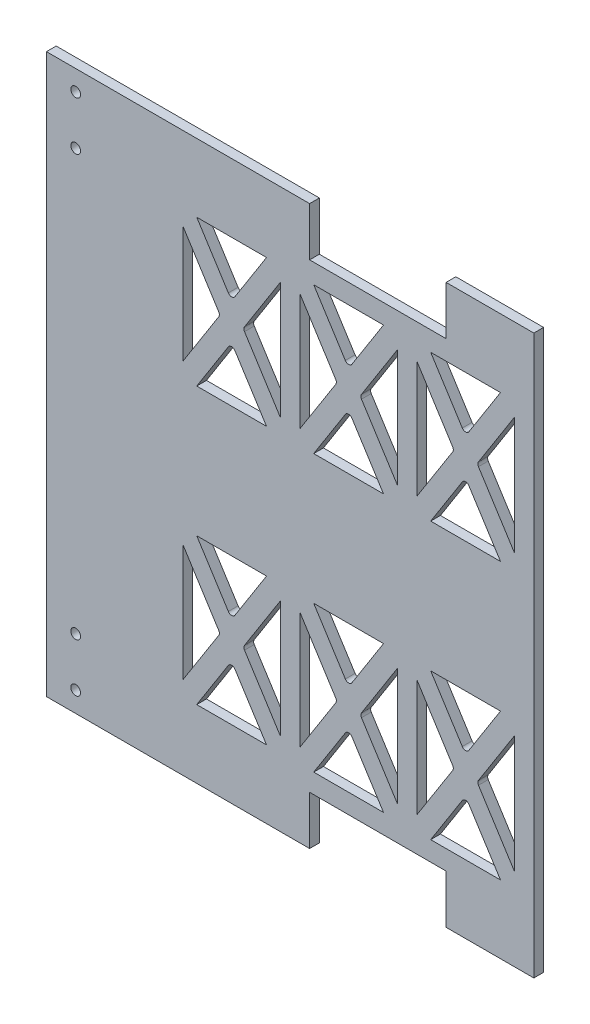
SolidWorks part; units mm, degrees
material "Acrylic (Medium-high impact)"
ref_plane "Front Plane" through (0, 0, 0) normal (0, 0, 1) x (1, 0, 0)
ref_plane "Top Plane" through (0, 0, 0) normal (0, 1, 0) x (1, 0, 0)
ref_plane "Right Plane" through (0, 0, 0) normal (1, 0, 0) x (0, 0, -1)
sketch "Sketch2" plane through (0, 0, 0) normal (0, 0, 1) x (1, 0, 0)
  line L1 (-125, 143.25) -> (125, 143.25)
  line L2 (-125, 143.25) -> (-125, -143.25)
  line L3 (-125, -143.25) -> (125, -143.25)
  line L4 (125, 143.25) -> (125, -143.25)
  line L5 (-125, 143.25) -> (125, -143.25) construction
  line L6 (-125, -143.25) -> (125, 143.25) construction
  point P0 (0, 0)
  dimension "D1" = 250
  dimension "D2" = 286.5
extrude "Boss-Extrude1" add sketch "Sketch2" along normal blind 5
sketch "Sketch3" plane through (0, 0, 5) normal (0, 0, 1) x (1, 0, 0)
  line L0 (-125, 143.25) -> (-125, -143.25) construction
  line L1 (125, 143.25) -> (-125, 143.25) construction
  line L2 (-125, -143.25) -> (125, -143.25) construction
  line L3 (-125, 0) -> (125, 0) construction
  line L4 (125, -143.25) -> (125, 143.25) construction
  line L5 (10, 143.25) -> (80, 143.25)
  line L6 (10, 143.25) -> (10, 118.25)
  line L7 (10, 118.25) -> (80, 118.25)
  line L8 (80, 143.25) -> (80, 118.25)
  line L9 (10, -118.25) -> (80, -118.25)
  line L10 (80, -143.25) -> (80, -118.25)
  line L11 (10, -143.25) -> (80, -143.25)
  line L12 (10, -143.25) -> (10, -118.25)
  line L13 (107.9031, 108.25) -> (91.6881, 82.7301)
  line L14 (65, 108.25) -> (115, 108.25)
  line L15 (65, 108.25) -> (65, 33.25)
  line L16 (65, 33.25) -> (115, 33.25)
  line L17 (115, 108.25) -> (115, 33.25)
  line L18 (72.0969, 33.25) -> (88.3119, 58.7699)
  line L19 (65, 70.75) -> (115, 70.75) construction
  line L20 (72.0969, 108.25) -> (88.3119, 82.7301)
  line L21 (107.9031, 33.25) -> (91.6881, 58.7699)
  line L22 (96.6054, 69.6774) -> (115, 40.7272)
  line L23 (83.3946, 71.8226) -> (65, 100.7728)
  line L24 (83.3946, 69.6774) -> (65, 40.7272)
  line L25 (96.6054, 71.8226) -> (115, 100.7728)
  line L26 (5, 108.25) -> (5, 33.25)
  line L27 (5, 108.25) -> (55, 108.25)
  line L28 (55, 108.25) -> (55, 33.25)
  line L29 (5, 33.25) -> (55, 33.25)
  line L30 (12.0969, 33.25) -> (28.3119, 58.7699)
  line L31 (23.3946, 69.6774) -> (5, 40.7272)
  line L32 (47.9031, 33.25) -> (31.6881, 58.7699)
  line L33 (36.6054, 69.6774) -> (55, 40.7272)
  line L34 (36.6054, 71.8226) -> (55, 100.7728)
  line L35 (47.9031, 108.25) -> (31.6881, 82.7301)
  line L36 (12.0969, 108.25) -> (28.3119, 82.7301)
  line L37 (23.3946, 71.8226) -> (5, 100.7728)
  line L38 (-55, 108.25) -> (-55, 33.25)
  line L39 (-55, 108.25) -> (-5, 108.25)
  line L40 (-5, 108.25) -> (-5, 33.25)
  line L41 (-55, 33.25) -> (-5, 33.25)
  line L42 (-47.9031, 33.25) -> (-31.6881, 58.7699)
  line L43 (-36.6054, 69.6774) -> (-55, 40.7272)
  line L44 (-12.0969, 33.25) -> (-28.3119, 58.7699)
  line L45 (-23.3946, 69.6774) -> (-5, 40.7272)
  line L46 (-23.3946, 71.8226) -> (-5, 100.7728)
  line L47 (-12.0969, 108.25) -> (-28.3119, 82.7301)
  line L48 (-47.9031, 108.25) -> (-31.6881, 82.7301)
  line L49 (-36.6054, 71.8226) -> (-55, 100.7728)
  line L62 (5, -33.25) -> (5, -108.25)
  line L63 (5, -33.25) -> (55, -33.25)
  line L64 (55, -33.25) -> (55, -108.25)
  line L65 (5, -108.25) -> (55, -108.25)
  line L66 (12.0969, -108.25) -> (28.3119, -82.7301)
  line L67 (23.3946, -71.8226) -> (5, -100.7728)
  line L68 (47.9031, -108.25) -> (31.6881, -82.7301)
  line L69 (36.6054, -71.8226) -> (55, -100.7728)
  line L70 (36.6054, -69.6774) -> (55, -40.7272)
  line L71 (47.9031, -33.25) -> (31.6881, -58.7699)
  line L72 (12.0969, -33.25) -> (28.3119, -58.7699)
  line L73 (23.3946, -69.6774) -> (5, -40.7272)
  line L74 (-55, -33.25) -> (-55, -108.25)
  line L75 (-55, -33.25) -> (-5, -33.25)
  line L76 (-5, -33.25) -> (-5, -108.25)
  line L77 (-55, -108.25) -> (-5, -108.25)
  line L78 (-47.9031, -108.25) -> (-31.6881, -82.7301)
  line L79 (-36.6054, -71.8226) -> (-55, -100.7728)
  line L80 (-12.0969, -108.25) -> (-28.3119, -82.7301)
  line L81 (-23.3946, -71.8226) -> (-5, -100.7728)
  line L82 (-23.3946, -69.6774) -> (-5, -40.7272)
  line L83 (-12.0969, -33.25) -> (-28.3119, -58.7699)
  line L84 (-47.9031, -33.25) -> (-31.6881, -58.7699)
  line L85 (-36.6054, -69.6774) -> (-55, -40.7272)
  line L98 (65, -33.25) -> (65, -108.25)
  line L99 (65, -33.25) -> (115, -33.25)
  line L100 (115, -33.25) -> (115, -108.25)
  line L101 (65, -108.25) -> (115, -108.25)
  line L102 (72.0969, -108.25) -> (88.3119, -82.7301)
  line L103 (83.3946, -71.8226) -> (65, -100.7728)
  line L104 (107.9031, -108.25) -> (91.6881, -82.7301)
  line L105 (96.6054, -71.8226) -> (115, -100.7728)
  line L106 (96.6054, -69.6774) -> (115, -40.7272)
  line L107 (107.9031, -33.25) -> (91.6881, -58.7699)
  line L108 (72.0969, -33.25) -> (88.3119, -58.7699)
  line L109 (83.3946, -69.6774) -> (65, -40.7272)
  line L110 (-115, -33.25) -> (-65, -33.25) [skipped]
  line L111 (-96.6054, -71.8226) -> (-115, -100.7728) [skipped]
  line L112 (-83.3946, -71.8226) -> (-65, -100.7728) [skipped]
  line L113 (-83.3946, -69.6774) -> (-65, -40.7272) [skipped]
  line L114 (-72.0969, -33.25) -> (-88.3119, -58.7699) [skipped]
  line L115 (-107.9031, -33.25) -> (-91.6881, -58.7699) [skipped]
  line L116 (-96.6054, -69.6774) -> (-115, -40.7272) [skipped]
  line L117 (-115, -33.25) -> (-115, -108.25) [skipped]
  line L118 (-115, -108.25) -> (-65, -108.25) [skipped]
  line L119 (-65, -33.25) -> (-65, -108.25) [skipped]
  line L120 (-72.0969, -108.25) -> (-88.3119, -82.7301) [skipped]
  line L121 (-107.9031, -108.25) -> (-91.6881, -82.7301) [skipped]
  line L122 (-115, 33.25) -> (-65, 33.25) [skipped]
  line L123 (-107.9031, 33.25) -> (-91.6881, 58.7699) [skipped]
  line L124 (-96.6054, 69.6774) -> (-115, 40.7272) [skipped]
  line L125 (-72.0969, 33.25) -> (-88.3119, 58.7699) [skipped]
  line L126 (-83.3946, 69.6774) -> (-65, 40.7272) [skipped]
  line L127 (-115, 108.25) -> (-115, 33.25) [skipped]
  line L128 (-65, 108.25) -> (-65, 33.25) [skipped]
  line L129 (-115, 108.25) -> (-65, 108.25) [skipped]
  line L130 (-72.0969, 108.25) -> (-88.3119, 82.7301) [skipped]
  line L131 (-83.3946, 71.8226) -> (-65, 100.7728) [skipped]
  line L132 (-107.9031, 108.25) -> (-91.6881, 82.7301) [skipped]
  line L133 (-96.6054, 71.8226) -> (-115, 100.7728) [skipped]
  circle A0 centre (-110, -132.85) radius 2.5
  circle A2 centre (-110, -107.85) radius 2.5
  circle A4 centre (-110, 132.85) radius 2.5
  circle A5 centre (-110, 107.85) radius 2.5
  arc A6 (83.3946, 71.8226) -> (83.3946, 69.6774) centre (81.7065, 70.75) cw
  arc A7 (91.6881, 58.7699) -> (88.3119, 58.7699) centre (90, 57.6973) ccw
  arc A8 (96.6054, 69.6774) -> (96.6054, 71.8226) centre (98.2935, 70.75) cw
  arc A9 (91.6881, 82.7301) -> (88.3119, 82.7301) centre (90, 83.8027) cw
  arc A10 (23.3946, 71.8226) -> (23.3946, 69.6774) centre (21.7065, 70.75) cw
  arc A11 (36.6054, 69.6774) -> (36.6054, 71.8226) centre (38.2935, 70.75) cw
  arc A12 (31.6881, 58.7699) -> (28.3119, 58.7699) centre (30, 57.6973) ccw
  arc A13 (31.6881, 82.7301) -> (28.3119, 82.7301) centre (30, 83.8027) cw
  arc A14 (-36.6054, 71.8226) -> (-36.6054, 69.6774) centre (-38.2935, 70.75) cw
  arc A15 (-23.3946, 69.6774) -> (-23.3946, 71.8226) centre (-21.7065, 70.75) cw
  arc A16 (-28.3119, 58.7699) -> (-31.6881, 58.7699) centre (-30, 57.6973) ccw
  arc A17 (-28.3119, 82.7301) -> (-31.6881, 82.7301) centre (-30, 83.8027) cw
  arc A22 (23.3946, -69.6774) -> (23.3946, -71.8226) centre (21.7065, -70.75) cw
  arc A23 (36.6054, -71.8226) -> (36.6054, -69.6774) centre (38.2935, -70.75) cw
  arc A24 (31.6881, -82.7301) -> (28.3119, -82.7301) centre (30, -83.8027) ccw
  arc A25 (31.6881, -58.7699) -> (28.3119, -58.7699) centre (30, -57.6973) cw
  arc A26 (-36.6054, -69.6774) -> (-36.6054, -71.8226) centre (-38.2935, -70.75) cw
  arc A27 (-23.3946, -71.8226) -> (-23.3946, -69.6774) centre (-21.7065, -70.75) cw
  arc A28 (-28.3119, -82.7301) -> (-31.6881, -82.7301) centre (-30, -83.8027) ccw
  arc A29 (-28.3119, -58.7699) -> (-31.6881, -58.7699) centre (-30, -57.6973) cw
  arc A34 (83.3946, -69.6774) -> (83.3946, -71.8226) centre (81.7065, -70.75) cw
  arc A35 (96.6054, -71.8226) -> (96.6054, -69.6774) centre (98.2935, -70.75) cw
  arc A36 (91.6881, -82.7301) -> (88.3119, -82.7301) centre (90, -83.8027) ccw
  arc A37 (91.6881, -58.7699) -> (88.3119, -58.7699) centre (90, -57.6973) cw
  arc A38 (-96.6054, -69.6774) -> (-96.6054, -71.8226) centre (-98.2935, -70.75) cw [skipped]
  arc A39 (-83.3946, -71.8226) -> (-83.3946, -69.6774) centre (-81.7065, -70.75) cw [skipped]
  arc A40 (-88.3119, -82.7301) -> (-91.6881, -82.7301) centre (-90, -83.8027) ccw [skipped]
  arc A41 (-88.3119, -58.7699) -> (-91.6881, -58.7699) centre (-90, -57.6973) cw [skipped]
  arc A42 (-96.6054, 71.8226) -> (-96.6054, 69.6774) centre (-98.2935, 70.75) cw [skipped]
  arc A43 (-83.3946, 69.6774) -> (-83.3946, 71.8226) centre (-81.7065, 70.75) cw [skipped]
  arc A44 (-88.3119, 58.7699) -> (-91.6881, 58.7699) centre (-90, 57.6973) ccw [skipped]
  arc A45 (-88.3119, 82.7301) -> (-91.6881, 82.7301) centre (-90, 83.8027) cw [skipped]
  point P46 (84.0761, 70.75)
  point P51 (95.9239, 70.75)
  point P54 (90, 80.0733)
  point P55 (-30, 33.25)
  line M2 (125, 143.25) -> (-125, 143.25)
  line M4 (-125, -143.25) -> (125, -143.25)
  dimension "D1" = 5
  dimension "D3" = 10.4
  dimension "D4" = 25
  dimension "D5" = 70
  dimension "D8" = 5
  dimension "D17" = 2
  dimension "D2" = 15
  dimension "D6" = 25
  dimension "D7" = 45
  dimension "D9" = 15
  dimension "D10" = 50
  dimension "D11" = 75
  dimension "D12" = 10
  dimension "D13" = 10
  dimension "D14" = 10
  dimension "D15" = 80
  dimension "D16" = 25
  dimension "D20" = 10
  dimension "D21" = 66.5
  dimension "D22" = 10
  dimension "D18" = 4
  dimension "D19" = 2
extrude "Cut-Extrude1" cut sketch "Sketch3" against normal blind 5 contours A0 | A2 | A4 | A5 | L12 L10 L9 M4 | L8 L6 L7 M2 | L32 A12 L30 L29 | A10 L37 L26 L31 | A13 L35 L27 L36 | A17 L47 L39 L48 | A15 L45 L40 L46 | A14 L49 L38 L43 | L44 A16 L42 L41 | A11 L33 L28 L34 | A29 L83 L75 L84 | A26 L85 L74 L79 | L80 A28 L78 L77 | A27 L81 L76 L82 | A22 L73 L62 L67 | A25 L71 L63 L72 | A23 L69 L64 L70 | L68 A24 L66 L65 | A34 L109 L98 L103 | A37 L107 L99 L108 | A35 L105 L100 L106 | L104 A36 L102 L101 | A8 L22 L17 L25 | A9 L13 L14 L20 | A6 L23 L15 L24 | L21 A7 L18 L16
